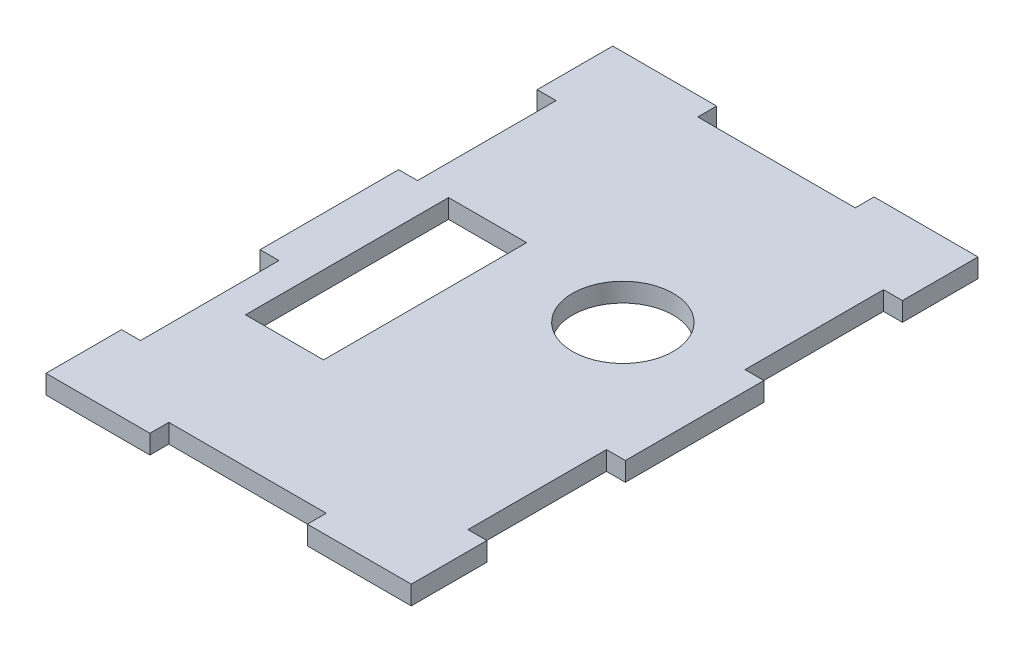
SolidWorks part; units mm, degrees
ref_plane "Front Plane" through (0, 0, 0) normal (0, 0, 1) x (1, 0, 0)
ref_plane "Top Plane" through (0, 0, 0) normal (0, 1, 0) x (1, 0, 0)
ref_plane "Right Plane" through (0, 0, 0) normal (1, 0, 0) x (0, 0, -1)
sketch "Sketch3" plane through (0, 0, 0) normal (0, 1, 0) x (1, 0, 0)
  arc B0 (-9.3, -50.5812) -> (-14.7, -50.5812) centre (-12, -45) ccw
  line B1 (-5.8, -66.125) -> (-5.8, -33.875)
  arc B2 (-12.5, -34.875) -> (-11.5, -34.875) centre (-12, -35.8548) ccw
  line B3 (-5.8, -38.7) -> (-18.2, -38.7)
  circle B4 centre (-12, -45) radius 2.45
  circle B5 centre (-12, -45) radius 0.6
  line B6 (-11.5, -33.875) -> (-5.8, -33.875)
  arc B7 (-11.5, -65.125) -> (-12.5, -65.125) centre (-12, -64.1452) ccw
  line B8 (-11.5, -66.125) -> (-5.8, -66.125)
  line B9 (-18.2, -33.875) -> (-12.5, -33.875)
  line B10 (-18.2, -33.875) -> (-18.2, -66.125)
  line B11 (-18.2, -61.3) -> (-5.8, -61.3)
  arc B12 (-14.7, -50.7) -> (-9.3, -50.7) centre (-12, -50.7) ccw
  line B13 (-18.2, -66.125) -> (-12.5, -66.125)
  line B14 (-9.3, -50.7) -> (-9.3, -50.5812)
  line B15 (-14.7, -50.7) -> (-14.7, -50.5812)
  line B16 (-12.5, -34.875) -> (-12.5, -33.875)
  line B17 (-11.5, -34.875) -> (-11.5, -33.875)
  line B18 (-11.5, -65.125) -> (-11.5, -66.125)
  line B19 (-12.5, -65.125) -> (-12.5, -66.125)
sketch_block_instance "Block1-4"
sketch_block "Block1"
other "DetailItem3"
other "DetailItem4" parameters "D1"=39.4834, "D2"=11.0212, "D3"=5.8
sketch "Sketch1" plane through (0, 0, 0) normal (0, 1, 0) x (1, 0, 0)
  line L0 (-18.2, -7.5092) -> (-18.2, -45)
  line L1 (-26, 0) -> (32, 0)
  line L2 (-26, 0) -> (-26, -90)
  line L3 (-26, -90) -> (32, -90)
  line L4 (32, 0) -> (32, -90)
  line L5 (25.4908, -51.2) -> (-12, -51.2)
  circle A0 centre (-4.2, -20.1976) radius 8.5
  arc A2 (-18.2, -7.5092) -> (25.4908, -51.2) centre (-12, -45) cw
  circle A3 centre (12.8024, -37.2) radius 8
  arc A5 (-18.2, -45) -> (-12, -51.2) centre (-12, -45) ccw
  dimension "D3" = 17
  dimension "D6" = 6.2
  dimension "D10" = 6.2
  dimension "D8" = 16
  dimension "D1" = 58
  dimension "D2" = 90
  dimension "D4" = 38
  dimension "D5" = 6.2
  dimension "D7" = 26
  dimension "D9" = 26
  dimension "D11" = 14
  dimension "D12" = 14
  dimension "D13" = 32
sketch "Sketch4" plane through (0, 0, 0) normal (0, 1, 0) x (1, 0, 0)
  line L0 (-26, -90) -> (32, -90) construction
  line L1 (32, 0) -> (32, -90) construction
  line L2 (-26, 0) -> (-26, -90) construction
  line L3 (-26, 0) -> (32, 0) construction
  line L4 (-26, -90) -> (-9.5, -90)
  line L5 (32, 0) -> (32, -12)
  line L6 (-26, 0) -> (-26, -12)
  line L7 (-26, 0) -> (-9.5, 0)
  line L8 (32, -12) -> (29, -12)
  line L9 (29, -12) -> (29, -34)
  line L10 (29, -34) -> (32, -34)
  line L11 (32, -34) -> (32, -56)
  line L12 (32, -78) -> (29, -78)
  line L13 (29, -78) -> (29, -56)
  line L14 (29, -56) -> (32, -56)
  line L15 (32, -78) -> (32, -90)
  line L16 (-26, -12) -> (-23, -12)
  line L17 (-23, -12) -> (-23, -34)
  line L18 (-23, -34) -> (-26, -34)
  line L19 (-26, -34) -> (-26, -56)
  line L20 (-26, -56) -> (-23, -56)
  line L21 (-23, -56) -> (-23, -78)
  line L22 (-23, -78) -> (-26, -78)
  line L23 (-26, -78) -> (-26, -90)
  line L24 (-9.5, 0) -> (-9.5, -3)
  line L25 (-9.5, -3) -> (15.5, -3)
  line L26 (15.5, -3) -> (15.5, 0)
  line L27 (15.5, 0) -> (32, 0)
  line L28 (-9.5, -90) -> (-9.5, -87)
  line L29 (-9.5, -87) -> (15.5, -87)
  line L30 (15.5, -87) -> (15.5, -90)
  line L31 (15.5, -90) -> (32, -90)
  line L40 (-18.2, -33.875) -> (-18.2, -66.125) construction
  line L41 (-5.8, -66.125) -> (-5.8, -33.875) construction
  line L42 (-18.2, -33.875) -> (-18.2, -66.125)
  line L43 (-5.8, -66.125) -> (-5.8, -33.875)
  line L44 (-18.2, -33.875) -> (-5.8, -33.875)
  line L45 (-18.2, -66.125) -> (-5.8, -66.125)
  circle A10 centre (12.8024, -37.2) radius 8
  dimension "D18" = 16
  dimension "D2" = 12
  dimension "D3" = 22
  dimension "D4" = 3
  dimension "D5" = 12
  dimension "D6" = 22
  dimension "D7" = 3
  dimension "D8" = 12
  dimension "D9" = 12
  dimension "D10" = 22
  dimension "D11" = 22
  dimension "D12" = 3
  dimension "D13" = 25
  dimension "D14" = 16.5
  dimension "D15" = 16.5
  dimension "D16" = 25
  dimension "D17" = 3
sketch "Sketch7" [suppressed] plane through (0, 0, 0) normal (0, 1, 0) x (1, 0, 0)
  line L0 (25.4908, -51.2) -> (-12, -51.2) construction
  line L1 (-18.2, -7.5092) -> (-18.2, -45) construction
  line L2 (25.4908, -51.2) -> (-12, -51.2)
  line L3 (-18.2, -7.5092) -> (-18.2, -45)
  arc A0 (-18.2, -45) -> (-12, -51.2) centre (-12, -45) ccw construction
  circle A1 centre (-12, -45) radius 1.5 construction
  circle A2 centre (-4.2, -20.1976) radius 8.5 construction
  circle A3 centre (12.8024, -37.2) radius 8.5 construction
  arc A4 (25.4908, -51.2) -> (-18.2, -7.5092) centre (-12, -45) ccw construction
  arc A5 (-18.2, -45) -> (-12, -51.2) centre (-12, -45) ccw
  circle A6 centre (-12, -45) radius 1.5
  circle A7 centre (-4.2, -20.1976) radius 8.5
  circle A8 centre (12.8024, -37.2) radius 8.5
  arc A9 (25.4908, -51.2) -> (-18.2, -7.5092) centre (-12, -45) ccw
extrude "Boss-Extrude2" add sketch "Sketch4" along normal blind 3
